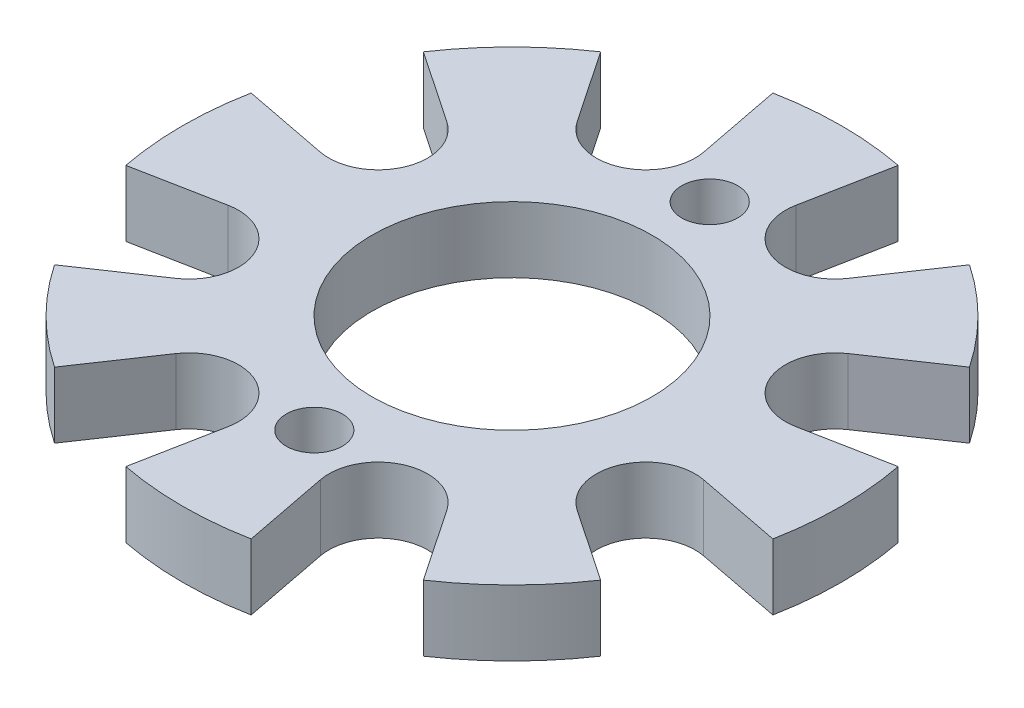
SolidWorks part; units mm, degrees
material "Acrylic (Medium-high impact)"
ref_plane "Front Plane" through (0, 0, 0) normal (0, 0, 1) x (1, 0, 0)
ref_plane "Top Plane" through (0, 0, 0) normal (0, 1, 0) x (1, 0, 0)
ref_plane "Right Plane" through (0, 0, 0) normal (1, 0, 0) x (0, 0, -1)
sketch "Sketch1" plane through (0, 0, 0) normal (0, 1, 0) x (1, 0, 0)
  circle A0 centre (0, 0) radius 20
  dimension "D1" = 40
sketch "Sketch2" plane through (0, 0, 0) normal (0, 1, 0) x (1, 0, 0)
  line L0 (-11.8283, 0) -> (13.8416, 0) construction
  circle A0 centre (0, 0) radius 4
  circle A1 centre (0, 12) radius 1.7
  circle A2 centre (0, -12) radius 1.7
  dimension "D1" = 8
  dimension "D2" = 3.4
  dimension "D3" = 12
extrude "Boss-Extrude1" add sketch "Sketch1" along normal blind 4
extrude "Cut-Extrude1" cut sketch "Sketch2" along normal up to next
sketch "Sketch3" plane through (0, 0, 0) normal (0, 1, 0) x (1, 0, 0)
  line L0 (0, 0) -> (0, 20) construction
  line L1 (0, 0) -> (7.6537, 18.4776) construction
  line L2 (3.8035, 19.635) -> (2.795, 14.4287)
  line L3 (11.1946, 16.5735) -> (8.2263, 12.179)
  line L4 (2.795, 14.4287) -> (8.2263, 12.179) construction
  circle A1 centre (0, 0) radius 4 construction
  circle A2 centre (0, 0) radius 20 construction
  arc A3 (2.795, 14.4287) -> (8.2263, 12.179) centre (5.7403, 13.8582) ccw
  arc A4 (3.8035, 19.635) -> (11.1946, 16.5735) centre (0, 0) cw
  point P0 (0, 0)
  dimension "D2" = 3
  dimension "D1" = 15
  dimension "D3" = 22.5
extrude "Cut-Extrude3" cut sketch "Sketch3" along normal up to next (4 mm away) contours A4 L2 A3 L3
pattern_circular "CirPattern1" count 8 over 360 about axis through (0, 0, 0) along (0, 1, 0) of "Cut-Extrude3"
sketch "Sketch4" plane through (0, 4, 0) normal (0, 1, 0) x (1, 0, 0)
  circle A0 centre (0, 0) radius 8.5
  dimension "D1" = 17
extrude "Cut-Extrude4" cut sketch "Sketch4" against normal through all
